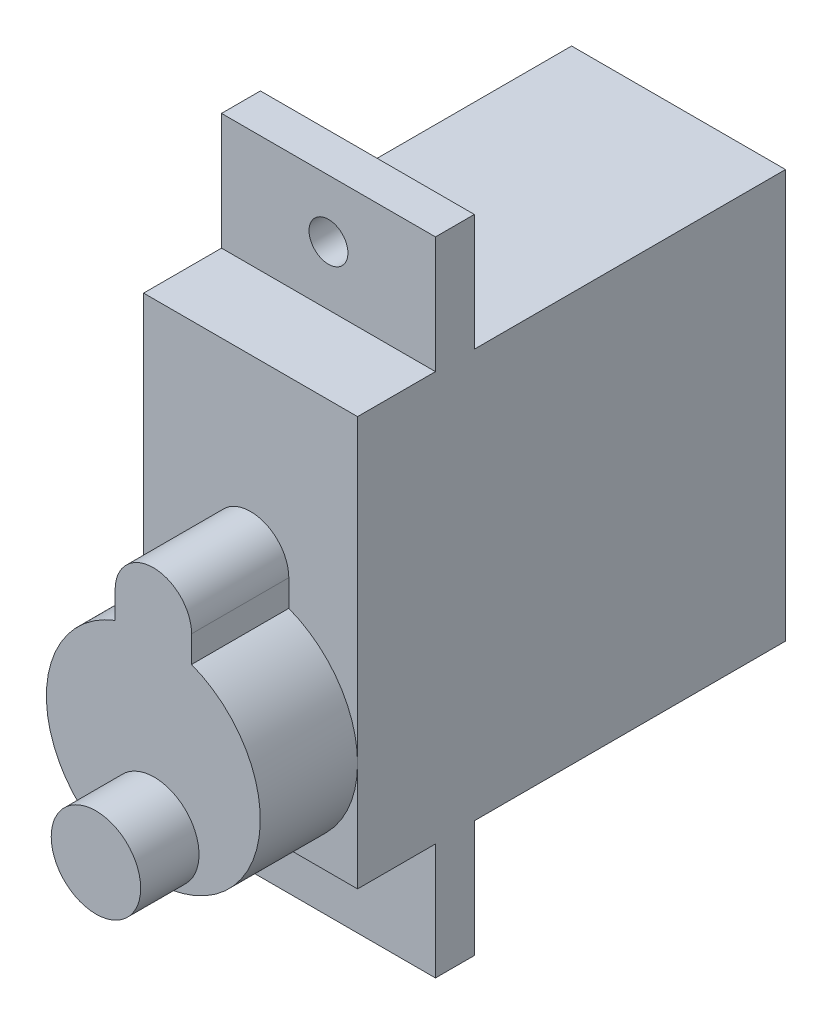
SolidWorks part; units mm, degrees
material "Acrílico (Impacto medio-alto)"
ref_plane "Alzado" through (0, 0, 0) normal (0, 0, 1) x (1, 0, 0)
ref_plane "Planta" through (0, 0, 0) normal (0, 1, 0) x (1, 0, 0)
ref_plane "Vista lateral" through (0, 0, 0) normal (1, 0, 0) x (0, 0, -1)
sketch "Croquis1" plane through (0, 0, 0) normal (0, 0, 1) x (1, 0, 0)
  line L1 (-5.5, 16.5) -> (5.5, 16.5)
  line L2 (-5.5, 16.5) -> (-5.5, -16.5)
  line L3 (-5.5, -16.5) -> (5.5, -16.5)
  line L4 (5.5, 16.5) -> (5.5, -16.5)
  line L5 (-5.5, 16.5) -> (5.5, -16.5) construction
  line L6 (-5.5, -16.5) -> (5.5, 16.5) construction
  point P0 (0, 0)
extrude "Saliente-Extruir1" add sketch "Croquis1" along normal blind 33
sketch "Croquis2" plane through (0, -16.5, 0) normal (0, -1, 0) x (1, 0, 0)
  line L0 (0, 0) -> (0, 17) construction
  line L1 (-5.5, 17) -> (5.5, 17)
  line L2 (5.5, 33) -> (5.5, 0) construction
  line L3 (5.5, 17) -> (5.5, 0)
  line L4 (5.5, 0) -> (-5.5, 0)
  line L5 (-5.5, 17) -> (-5.5, 0)
extrude "Cortar-Extruir1" cut sketch "Croquis2" against normal blind 6
mirror "Simetría1" about plane through (0, 0, 0) normal (0, 1, 0) of "Cortar-Extruir1"
sketch "Croquis3" plane through (5.5, 0, 0) normal (1, 0, 0) x (0, 0, -1)
  line L0 (-17, -16.5) -> (-19, -16.5) construction
  line L1 (-33, -16.5) -> (-17, -16.5) construction
  line L2 (-19, -16.5) -> (-19, -13.5)
  line L4 (-33, -16.5) -> (-33, 16.5) construction
  line L5 (-33, -13.5) -> (-33, -16.5)
  line L7 (-17, 16.5) -> (-19, 16.5) construction
  line L8 (-33, 16.5) -> (-17, 16.5) construction
  line L9 (-19, 16.5) -> (-19, 0.5)
  line L13 (-19, 16.5) -> (-23.0051, 16.5)
  line L14 (-23.0051, 16.5) -> (-23.0051, 0.5)
  line L15 (-23.0051, 0.5) -> (-19, 0.5)
  line L16 (-23.0051, -13.5) -> (-23.0051, -16.5)
  line L17 (-23.0051, -13.5) -> (-33, -13.5)
  line L18 (-23.0051, 0.5) -> (-33, 0.5)
  line L19 (-33, 0.5) -> (-33, 16.5)
  line L20 (-33, 16.5) -> (-23.0051, 16.5)
  line L21 (-33, -16.5) -> (-23.0051, -16.5)
  line L22 (-23.0051, -13.5) -> (-19, -13.5)
  line L23 (-23.0051, -16.5) -> (-19, -16.5)
  line L24 (-23.0051, 16.5) -> (-23.0051, 13.5333)
  line L25 (-23.0051, 13.5333) -> (-19, 13.5333)
  line L26 (-19, 13.5333) -> (-19, 16.5)
  line L27 (-23.0051, 0.5) -> (-23.0051, -13.5)
  line L28 (-33, -13.5) -> (-33, 0.5)
  line L29 (-17, 10.5) -> (-19, 10.5) construction
  line L30 (-19, 10.5) -> (-23.0051, 10.5)
  line L31 (-19, -13.5) -> (-19, -10.5309)
  line L32 (-19, -10.5309) -> (-33, -10.5309)
  line L33 (-33, -10.5309) -> (-33, -13.5)
  line L34 (-23.0051, -13.5) -> (-23.0051, -10.5309)
  line L35 (-23.0051, -10.5309) -> (-23.0051, -13.5)
  line M5 (-17, 16.5) -> (-33, 16.5)
  line M6 (-33, 16.5) -> (-33, -16.5)
  line M7 (-33, -16.5) -> (-17, -16.5)
extrude "Cortar-Extruir2" cut sketch "Croquis3" against normal up to next contours L18 L14 M5 M6 | L16 L17 M6 M7 | L14 L25 L9 M5 | L27 L18 L17 M6 | L22 L16 L2 M7 | L30 L9 L25 L14 | L31 L32 L27 L22 | L27 L32 L28 L17
sketch "Croquis6" plane through (0, 0, 23.0051) normal (0, 0, 1) x (1, 0, 0)
  line L0 (0, -10.4423) -> (0, 3.5577) construction
  line L1 (0, 0.5577) -> (5.5, 0.5577) construction
  line L2 (5.5, 10.5) -> (5.5, -10.5309) construction
  line L3 (0, 3.5577) -> (1.9646, 3.5577) construction
  line L4 (1.9646, 3.5577) -> (1.9646, 1.5599) construction
  line L5 (-1.9646, 1.5599) -> (-1.9646, 0.1948)
  line L6 (1.9646, 1.5599) -> (1.9646, 0.1948)
  circle A0 centre (0, -4.9423) radius 5.5 construction
  circle A1 centre (0, 1.5599) radius 1.9646 construction
  arc A2 (-1.9646, 1.5599) -> (1.9646, 1.5599) centre (0, 1.5599) cw
  arc A3 (-1.9646, 0.1948) -> (1.9646, 0.1948) centre (0, -4.9423) ccw
extrude "Saliente-Extruir4" add sketch "Croquis6" along normal blind 5
sketch "Croquis7" plane through (0, 0, 28.0051) normal (0, 0, 1) x (1, 0, 0)
  circle A0 centre (0.0484, -8.0791) radius 5.4072 construction
  circle A1 centre (0.0484, -8.0791) radius 2.3
extrude "Saliente-Extruir5" add sketch "Croquis7" along normal blind 3
sketch "Croquis8" plane through (0, 0, 19) normal (0, 0, 1) x (1, 0, 0)
  line L0 (0, 0) -> (0, -10.5309) construction
  line L2 (-5.5, -10.5309) -> (5.5, -10.5309) construction
  line L4 (0, 0) -> (5.5, 0) construction
  line L5 (5.5, 10.5) -> (5.5, -4.9423) construction
  line L6 (0, -10.5309) -> (0, -13.5309) construction
  circle A2 centre (0, -13.5309) radius 1
  circle A3 centre (0, 13.5309) radius 1
extrude "Cortar-Extruir4" cut sketch "Croquis8" against normal blind 3
sketch "Croquis9" plane through (5.5, 0, 0) normal (1, 0, 0) x (0, 0, -1)
  line L0 (0, 0) -> (0, -10.5) construction
  line L1 (0, 10.5) -> (-17, 10.5) construction
  line L2 (0, -10.5) -> (-1, -10.5)
  line L3 (0, -10.5) -> (0, 10.5)
  line L4 (0, 10.5) -> (-1, 10.5)
  line L5 (-1, -10.5) -> (-1, 10.5)
extrude "Cortar-Extruir5" cut sketch "Croquis9" against normal blind 20
